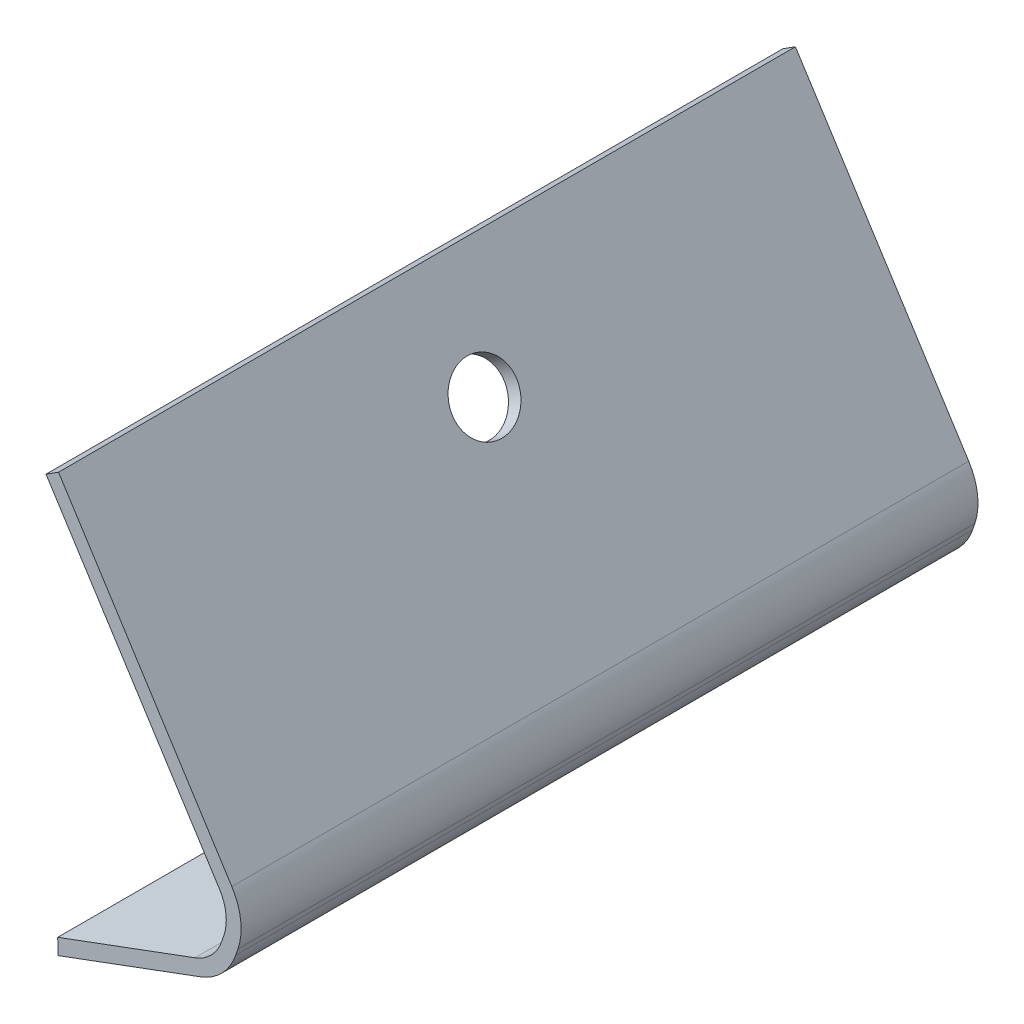
SolidWorks part; units mm, degrees
ref_plane "Front Plane" through (0, 0, 0) normal (0, 0, 1) x (1, 0, 0)
ref_plane "Top Plane" through (0, 0, 0) normal (0, 1, 0) x (1, 0, 0)
ref_plane "Right Plane" through (0, 0, 0) normal (1, 0, 0) x (0, 0, -1)
sketch "Sketch1" plane through (0, 0, 0) normal (0, 0, 1) x (1, 0, 0)
  line L0 (5.5372, 43.3324) -> (35.215, -3.286)
  line L1 (36.2593, -12.0253) -> (35.883, -13.1274)
  line L2 (29.8007, -19.3704) -> (5.4359, -28.4058)
  line L3 (3.3945, 41.9684) -> (33.0724, -4.6501)
  line L4 (33.8556, -11.2046) -> (33.4792, -12.3067)
  line L5 (28.9175, -16.9889) -> (5.4019, -25.7094)
  line L6 (29.8007, -19.3704) -> (6.285, -28.0909) construction
  line L7 (5.5372, 43.3324) -> (3.3945, 41.9684)
  line L8 (5.4019, -25.7094) -> (5.4359, -28.4058)
  arc A1 (36.2593, -12.0253) -> (35.215, -3.286) centre (26.6444, -8.7422) ccw
  arc A2 (35.883, -13.1274) -> (29.8007, -19.3704) centre (26.268, -9.8443) cw
  arc A3 (33.8556, -11.2046) -> (33.0724, -4.6501) centre (26.6444, -8.7422) ccw
  arc A4 (33.4792, -12.3067) -> (28.9175, -16.9889) centre (26.268, -9.8443) cw
  dimension "D1" = 10.16
  dimension "D2" = 2.54
extrude "Boss-Extrude1" add sketch "Sketch1" against normal up to surface (126.1872 mm away) from surface at -1.5748
sketch "Sketch2" plane through (23.5706, 15.0053, 0) normal (0.8436, 0.537, 0) x (0, 0, -1)
  circle A0 centre (64.6684, 15.2267) radius 5.5
  ellipse E0 centre (64.6684, 15.2267) end of major axis (70.1684, 15.2267) minor radius 5.5 (67.9129, 19.6678) -> (61.4239, 19.6678) ccw construction
  ellipse E1 centre (64.6684, 15.2267) end of major axis (70.1684, 15.2267) minor radius 5.5 (67.9129, 19.6678) -> (61.4239, 19.6678) ccw
extrude "Cut-Extrude1" cut sketch "Sketch2" against normal blind 63.5 contours A0
